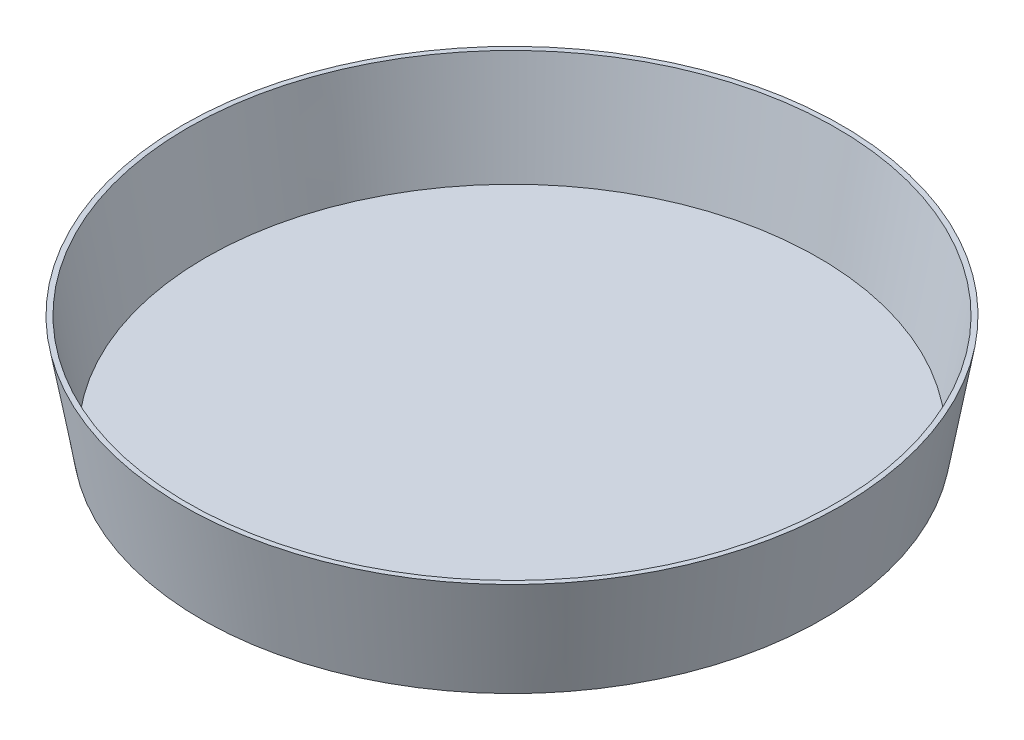
SolidWorks part; units mm, degrees
ref_plane "Front Plane" through (0, 0, 0) normal (0, 0, 1) x (1, 0, 0)
ref_plane "Top Plane" through (0, 0, 0) normal (0, 1, 0) x (1, 0, 0)
ref_plane "Right Plane" through (0, 0, 0) normal (1, 0, 0) x (0, 0, -1)
sketch "Sketch1" plane through (0, 0, 0) normal (0, 0, 1) x (1, 0, 0)
  line L0 (0, 0) -> (0, -63.5)
  line L1 (0, -63.5) -> (188.8032, -63.5)
  line L2 (188.8032, -63.5) -> (200, 0)
  line L3 (200, 0) -> (0, 0)
  dimension "D1" = 100
  dimension "D2" = 200
  dimension "D3" = 63.5
revolve "Revolve1" add sketch "Sketch1" angle 360 about L0
shell "Shell2" thickness 3
